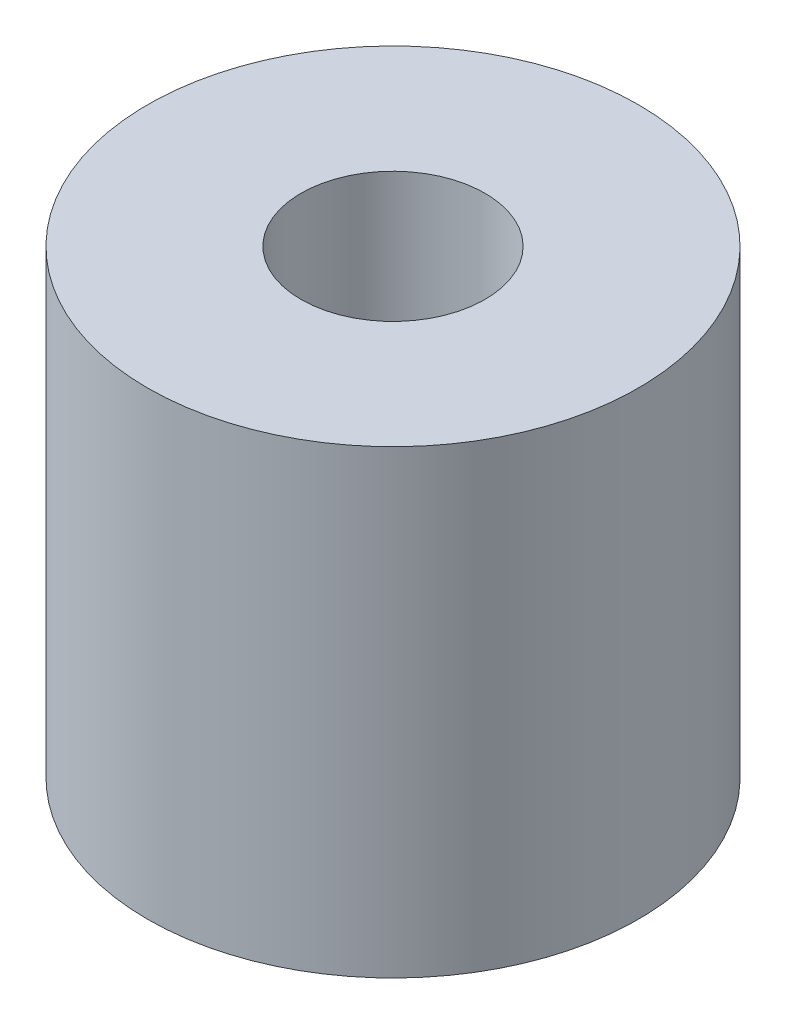
SolidWorks part; units mm, degrees
ref_plane "Front Plane" through (0, 0, 0) normal (0, 0, 1) x (1, 0, 0)
ref_plane "Top Plane" through (0, 0, 0) normal (0, 1, 0) x (1, 0, 0)
ref_plane "Right Plane" through (0, 0, 0) normal (1, 0, 0) x (0, 0, -1)
sketch "Sketch1" plane through (0, 0, 0) normal (0, 1, 0) x (1, 0, 0)
  circle A0 centre (0, 0) radius 0.6
  circle A1 centre (0, 0) radius 1.6
  dimension "D1" = 1.2
  dimension "D2" = 3.2
extrude "Boss-Extrude1" add sketch "Sketch1" along normal blind 3
